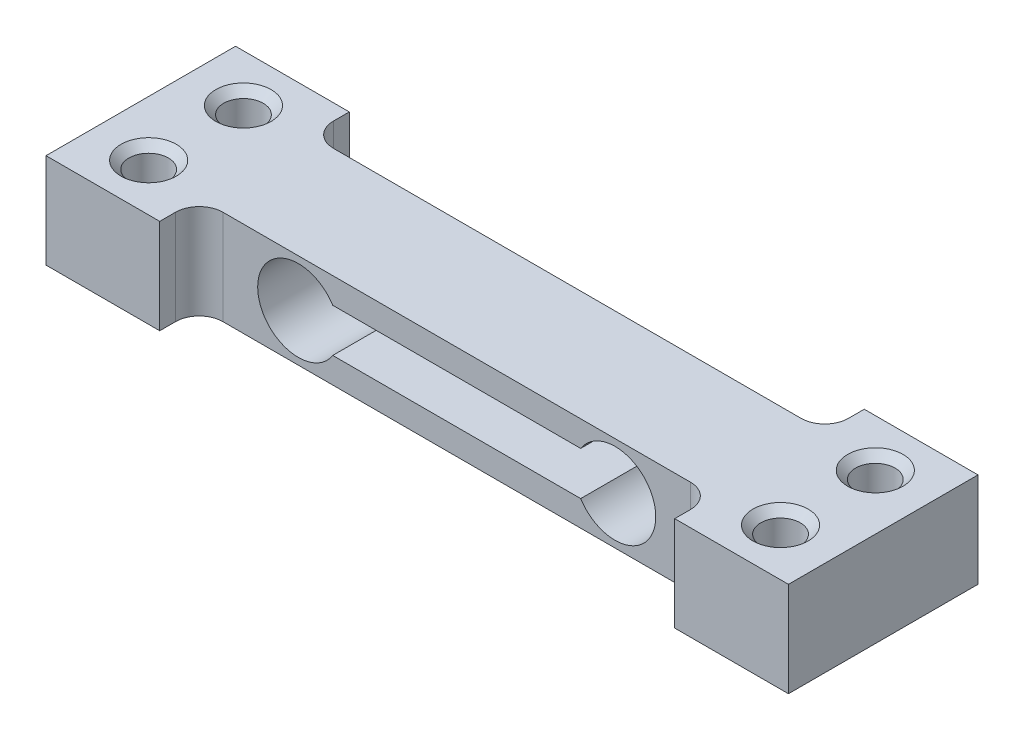
SolidWorks part; units mm, degrees
ref_plane "Front Plane" through (0, 0, 0) normal (0, 0, 1) x (1, 0, 0)
ref_plane "Top Plane" through (0, 0, 0) normal (0, 1, 0) x (1, 0, 0)
ref_plane "Right Plane" through (0, 0, 0) normal (1, 0, 0) x (0, 0, -1)
sketch "Sketch1" plane through (0, 0, 0) normal (0, 1, 0) x (1, 0, 0)
  line L0 (0, -3.5) -> (0, 3.5)
  line L1 (0, 3.5) -> (14.8, 3.5)
  line L2 (16.3, 5) -> (16.3, 6)
  line L3 (16.3, 6) -> (23.5, 6)
  line L4 (23.5, 6) -> (23.5, -6)
  line L5 (23.5, -6) -> (16.3, -6)
  line L6 (16.3, -5) -> (16.3, -6)
  line L7 (14.8, -3.5) -> (0, -3.5)
  line L8 (0, 0) -> (0, 50000) construction
  line L9 (0, 0) -> (50000, 0) construction
  arc A0 (14.8, 3.5) -> (16.3, 5) centre (14.8, 5) ccw
  arc A1 (16.3, -5) -> (14.8, -3.5) centre (14.8, -5) ccw
  point P4 (0, 0)
  dimension "D1" = 12
  dimension "D4" = 1.5
  dimension "D2" = 47
  dimension "D3" = 7
  dimension "D5" = 7.2
extrude "Boss-Extrude1" add sketch "Sketch1" along normal mid plane 6
sketch "Sketch2" plane through (0, 0, 3.5) normal (0, 0, 1) x (1, 0, 0)
  line L0 (0, 3) -> (0, -3) construction
  line L1 (-10.025, -1.375) -> (10.025, -1.375)
  line L2 (-10.025, -1.375) -> (-10.025, 1.375)
  line L3 (-10.025, 1.375) -> (10.025, 1.375)
  line L4 (10.025, -1.375) -> (10.025, 1.375)
  line L5 (-10.025, -1.375) -> (10.025, 1.375) construction
  line L6 (-10.025, 1.375) -> (10.025, -1.375) construction
  circle A0 centre (10.025, 0) radius 2.575
  point P0 (0, 0)
  line M6 (0, 3) -> (0, -3)
  dimension "D1" = 5.15
  dimension "D2" = 20.05
  dimension "D3" = 2.75
extrude "Cut-Extrude1" cut sketch "Sketch2" against normal through all contours L1 A0 L3 L4 | L3 A0 L1 L4 | A0 L3 L1 M6
sketch "Sketch3" plane through (0, 3, 0) normal (0, 1, 0) x (1, 0, 0)
  line L0 (0, 3.5) -> (0, -3.5) construction
  line L1 (-20, 3) -> (20, 3) construction
  line L2 (-20, 3) -> (-20, -3) construction
  line L3 (-20, -3) -> (20, -3) construction
  line L4 (20, 3) -> (20, -3) construction
  line L5 (-20, 3) -> (20, -3) construction
  line L6 (-20, -3) -> (20, 3) construction
  point P0 (0, 0)
  dimension "D1" = 40
  dimension "D2" = 6
hole_wizard "M3 Tapped Hole1" positions "Sketch4" profile "Sketch5" tap size "M3" standard "DIN" end condition through all
sketch "Sketch4" plane through (0, 3, 0) normal (0, 1, 0) x (1, 0, 0)
  point P0 (20, 3)
  point P3 (20, -3)
cosmetic thread "Hole Thread1" parameters "D2"=3
cosmetic thread "Hole Thread2" parameters "D2"=3
sketch "Sketch5" plane through (20, 3, -3) normal (1, 0, 0) x (0, 0, 1)
  line L0 (0, 0) -> (0, 6)
  line L1 (0, 6) -> (1.75, 6)
  line L2 (1.25, 5.5) -> (1.25, 0.5)
  line L3 (1.25, 0.5) -> (1.75, 0)
  line L5 (1.75, 0) -> (0, 0)
  line L6 (-1.25, 0.5) -> (-1.75, 0) construction
  line L7 (1.75, 6) -> (1.25, 5.5)
  line L8 (-1.75, 6) -> (-1.25, 5.5) construction
  line L11 (0, -6.35) -> (0, 107.95) construction
  dimension "Thru Tap Drill Dia." = 2.5
  dimension "Thru Tap Drill Depth" = 6
  dimension "Near C'Sink Dia." = 3.5
  dimension "Near C'Sink Angle" = 90
  dimension "Far C'Sink Dia." = 3.5
  dimension "Far C'Sink Angle" = 90
mirror "Mirror1" about plane through (0, 0, 0) normal (1, 0, 0) of bodies 103
